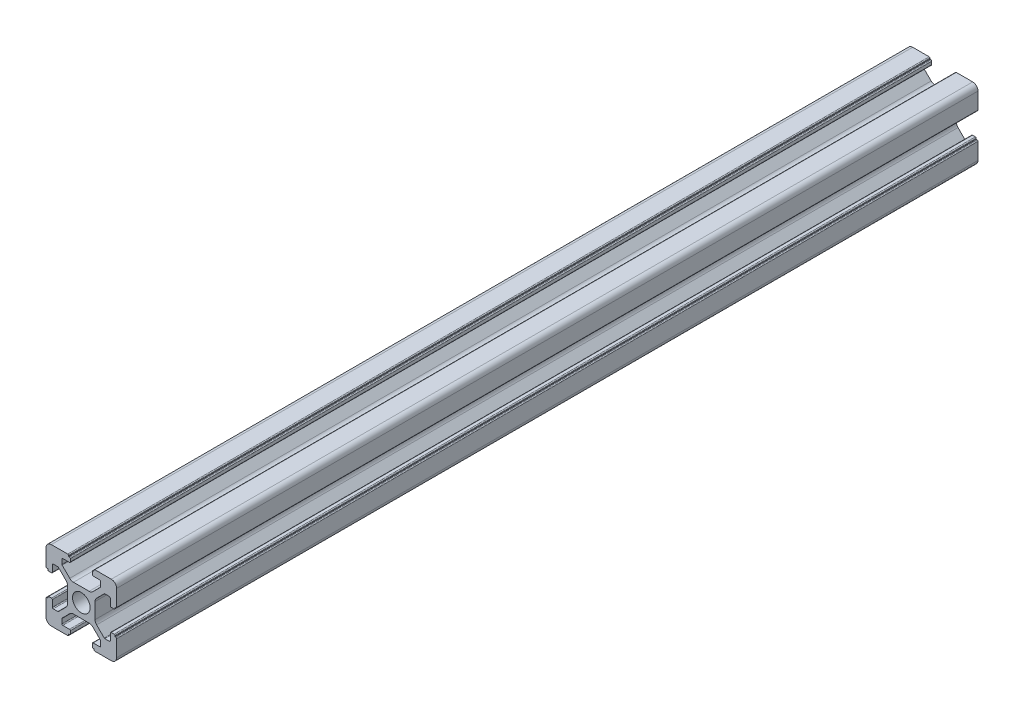
SolidWorks part; units mm, degrees
ref_plane "前视基准面" through (0, 0, 0) normal (0, 0, 1) x (1, 0, 0)
ref_plane "上视基准面" through (0, 0, 0) normal (0, 1, 0) x (1, 0, 0)
ref_plane "右视基准面" through (0, 0, 0) normal (1, 0, 0) x (0, 0, -1)
sketch "草图1" plane through (0, 0, 0) normal (0, 0, 1) x (1, 0, 0)
  line L0 (0, 0) -> (0, 5.5) construction
  line L1 (-8.5023, -10.0023) -> (-3.85, -10.0023)
  line L2 (-10.0023, -8.5023) -> (-10.0023, -3.85)
  line L3 (-8.5023, 10.0023) -> (-3.85, 10.0023)
  line L4 (10.0023, -8.5023) -> (10.0023, -3.85)
  line L5 (-10.0023, -10.0023) -> (10.0023, 10.0023) construction
  line L6 (-10.0023, 10.0023) -> (10.0023, -10.0023) construction
  line L7 (-2.218, -3.9) -> (2.218, -3.9)
  line L8 (-3.9, -2.218) -> (-3.9, 2.218)
  line L9 (-2.218, 3.9) -> (2.218, 3.9)
  line L10 (3.9, -2.218) -> (3.9, 2.218)
  line L11 (-3.9, -3.9) -> (3.9, 3.9) construction
  line L12 (-3.9, 3.9) -> (3.9, -3.9) construction
  line L13 (-5.25, -8.2) -> (-3.35, -8.2)
  line L14 (-8.2, -5.25) -> (-8.2, -3.35)
  line L15 (-5.25, 8.2) -> (-3.35, 8.2)
  line L16 (8.2, -5.25) -> (8.2, -3.35)
  line L17 (-8.2, -8.2) -> (8.2, 8.2) construction
  line L18 (-8.2, 8.2) -> (8.2, -8.2) construction
  line L19 (-7.95, 5.5) -> (-6.6642, 5.5)
  line L20 (0, 0) -> (5.5, 0) construction
  line L23 (-5.5, 7.95) -> (-5.5, 6.6642)
  line L26 (0, 0) -> (-0.5303, 0.5303)
  line L27 (3.2787, 4.3393) -> (5.4268, 6.4874)
  line L28 (0, 0) -> (0.5303, -0.5303)
  line L29 (5.5, 6.6642) -> (5.5, 7.95)
  line L30 (4.3393, 3.2787) -> (6.4874, 5.4268)
  line L31 (6.6642, 5.5) -> (7.95, 5.5)
  line L32 (4.3393, -3.2787) -> (6.4874, -5.4268)
  line L33 (3.2787, -4.3393) -> (5.4268, -6.4874)
  line L34 (-3.2787, -4.3393) -> (-5.4268, -6.4874)
  line L35 (-4.3393, -3.2787) -> (-6.4874, -5.4268)
  line L36 (-4.3393, 3.2787) -> (-6.4874, 5.4268)
  line L37 (-3.2787, 4.3393) -> (-5.4268, 6.4874)
  line L38 (3.1, -8.45) -> (3.1, -9.2523)
  line L39 (8.45, 3.1) -> (9.2523, 3.1)
  line L40 (-5.5, -6.6642) -> (-5.5, -7.95)
  line L41 (-6.6642, -5.5) -> (-7.95, -5.5)
  line L42 (5.5, -6.6642) -> (5.5, -7.95)
  line L43 (6.6642, -5.5) -> (7.95, -5.5)
  line L44 (9.2523, -3.1) -> (8.45, -3.1)
  line L46 (10.0023, 3.85) -> (10.0023, 8.5023)
  line L47 (8.2, 3.35) -> (8.2, 5.25)
  line L48 (-3.1, -9.2523) -> (-3.1, -8.45)
  line L49 (-8.45, -3.1) -> (-9.2523, -3.1)
  line L50 (-9.2523, 3.1) -> (-8.45, 3.1)
  line L51 (-3.1, 8.45) -> (-3.1, 9.2523)
  line L52 (3.1, 9.2523) -> (3.1, 8.45)
  line L53 (3.85, 10.0023) -> (8.5023, 10.0023)
  line L54 (3.35, 8.2) -> (5.25, 8.2)
  line L55 (-10.0023, 3.85) -> (-10.0023, 8.5023)
  line L56 (-8.2, 3.35) -> (-8.2, 5.25)
  line L57 (3.35, -8.2) -> (5.25, -8.2)
  line L58 (3.85, -10.0023) -> (8.5023, -10.0023)
  line L59 (9.7523, -3.6) -> (9.5023, -3.6)
  line L61 (9.7523, 3.6) -> (9.5023, 3.6)
  line L62 (9.5023, -3.6) -> (9.5023, -3.35)
  line L63 (3.6, -9.7523) -> (3.6, -9.5023)
  line L64 (3.35, -9.5023) -> (3.6, -9.5023)
  line L65 (9.5023, 3.35) -> (9.5023, 3.6)
  line L66 (-3.6, -9.5023) -> (-3.35, -9.5023)
  line L67 (-3.6, -9.7523) -> (-3.6, -9.5023)
  line L68 (-9.7523, -3.6) -> (-9.5023, -3.6)
  line L69 (-9.5023, -3.35) -> (-9.5023, -3.6)
  line L70 (-9.5023, 3.6) -> (-9.5023, 3.35)
  line L71 (-9.7523, 3.6) -> (-9.5023, 3.6)
  line L72 (-3.6, 9.7523) -> (-3.6, 9.5023)
  line L73 (-3.35, 9.5023) -> (-3.6, 9.5023)
  line L74 (3.6, 9.5023) -> (3.35, 9.5023)
  line L75 (3.6, 9.7523) -> (3.6, 9.5023)
  circle A0 centre (0, 0) radius 2.5
  arc A1 (10.0023, 8.5023) -> (8.5023, 10.0023) centre (8.5023, 8.5023) ccw
  arc A2 (8.5023, -10.0023) -> (10.0023, -8.5023) centre (8.5023, -8.5023) ccw
  arc A3 (-10.0023, -8.5023) -> (-8.5023, -10.0023) centre (-8.5023, -8.5023) ccw
  arc A4 (-10.0023, 8.5023) -> (-8.5023, 10.0023) centre (-8.5023, 8.5023) cw
  arc A5 (-9.5023, -3.35) -> (-9.2523, -3.1) centre (-9.2523, -3.35) cw
  arc A6 (-9.7523, -3.6) -> (-10.0023, -3.85) centre (-9.7523, -3.85) ccw
  arc A7 (-8.45, -3.1) -> (-8.2, -3.35) centre (-8.45, -3.35) cw
  arc A8 (-7.95, -5.5) -> (-8.2, -5.25) centre (-7.95, -5.25) cw
  arc A9 (-6.4874, -5.4268) -> (-6.6642, -5.5) centre (-6.6642, -5.25) cw
  arc A10 (-5.4268, -6.4874) -> (-5.5, -6.6642) centre (-5.25, -6.6642) ccw
  arc A11 (-5.5, -7.95) -> (-5.25, -8.2) centre (-5.25, -7.95) ccw
  arc A12 (-3.6, -9.7523) -> (-3.85, -10.0023) centre (-3.85, -9.7523) cw
  arc A13 (-3.35, -9.5023) -> (-3.1, -9.2523) centre (-3.35, -9.2523) ccw
  arc A14 (-3.1, -8.45) -> (-3.35, -8.2) centre (-3.35, -8.45) ccw
  arc A15 (3.1, -8.45) -> (3.35, -8.2) centre (3.35, -8.45) cw
  arc A16 (5.5, -7.95) -> (5.25, -8.2) centre (5.25, -7.95) cw
  arc A17 (5.4268, -6.4874) -> (5.5, -6.6642) centre (5.25, -6.6642) cw
  arc A18 (6.4874, -5.4268) -> (6.6642, -5.5) centre (6.6642, -5.25) ccw
  arc A19 (7.95, -5.5) -> (8.2, -5.25) centre (7.95, -5.25) ccw
  arc A20 (8.45, -3.1) -> (8.2, -3.35) centre (8.45, -3.35) ccw
  arc A21 (9.5023, -3.35) -> (9.2523, -3.1) centre (9.2523, -3.35) ccw
  arc A22 (9.7523, -3.6) -> (10.0023, -3.85) centre (9.7523, -3.85) cw
  arc A23 (3.35, -9.5023) -> (3.1, -9.2523) centre (3.35, -9.2523) cw
  arc A24 (3.6, -9.7523) -> (3.85, -10.0023) centre (3.85, -9.7523) ccw
  arc A25 (7.95, 5.5) -> (8.2, 5.25) centre (7.95, 5.25) cw
  arc A26 (8.2, 3.35) -> (8.45, 3.1) centre (8.45, 3.35) ccw
  arc A27 (9.5023, 3.35) -> (9.2523, 3.1) centre (9.2523, 3.35) cw
  arc A28 (9.7523, 3.6) -> (10.0023, 3.85) centre (9.7523, 3.85) ccw
  arc A29 (6.6642, 5.5) -> (6.4874, 5.4268) centre (6.6642, 5.25) ccw
  arc A30 (5.4268, 6.4874) -> (5.5, 6.6642) centre (5.25, 6.6642) ccw
  arc A31 (5.5, 7.95) -> (5.25, 8.2) centre (5.25, 7.95) ccw
  arc A32 (3.1, 8.45) -> (3.35, 8.2) centre (3.35, 8.45) ccw
  arc A33 (3.6, 9.7523) -> (3.85, 10.0023) centre (3.85, 9.7523) cw
  arc A34 (3.35, 9.5023) -> (3.1, 9.2523) centre (3.35, 9.2523) ccw
  arc A35 (-9.7523, 3.6) -> (-10.0023, 3.85) centre (-9.7523, 3.85) cw
  arc A36 (-9.5023, 3.35) -> (-9.2523, 3.1) centre (-9.2523, 3.35) ccw
  arc A37 (-8.45, 3.1) -> (-8.2, 3.35) centre (-8.45, 3.35) ccw
  arc A38 (-8.2, 5.25) -> (-7.95, 5.5) centre (-7.95, 5.25) cw
  arc A39 (-6.4874, 5.4268) -> (-6.6642, 5.5) centre (-6.6642, 5.25) ccw
  arc A40 (-5.4268, 6.4874) -> (-5.5, 6.6642) centre (-5.25, 6.6642) cw
  arc A41 (-5.5, 7.95) -> (-5.25, 8.2) centre (-5.25, 7.95) cw
  arc A42 (-3.1, 8.45) -> (-3.35, 8.2) centre (-3.35, 8.45) cw
  arc A43 (-3.1, 9.2523) -> (-3.35, 9.5023) centre (-3.35, 9.2523) ccw
  arc A44 (-3.6, 9.7523) -> (-3.85, 10.0023) centre (-3.85, 9.7523) ccw
  arc A45 (-4.3393, 3.2787) -> (-3.9, 2.218) centre (-5.4, 2.218) cw
  arc A46 (-3.2787, 4.3393) -> (-2.218, 3.9) centre (-2.218, 5.4) ccw
  arc A47 (3.2787, 4.3393) -> (2.218, 3.9) centre (2.218, 5.4) cw
  arc A48 (4.3393, 3.2787) -> (3.9, 2.218) centre (5.4, 2.218) ccw
  arc A49 (4.3393, -3.2787) -> (3.9, -2.218) centre (5.4, -2.218) cw
  arc A50 (3.2787, -4.3393) -> (2.218, -3.9) centre (2.218, -5.4) ccw
  arc A51 (-4.3393, -3.2787) -> (-3.9, -2.218) centre (-5.4, -2.218) ccw
  arc A52 (-2.218, -3.9) -> (-3.2787, -4.3393) centre (-2.218, -5.4) ccw
  point P0 (0, 0)
  point P7 (10.0023, 0)
  point P62 (0, 0)
  point P76 (0, 0)
  point P92 (-8.2, -5.5)
  point P99 (0, 0)
  point P106 (-5.5, -8.2)
  point P117 (5.5, -8.2)
  point P124 (8.2, -5.5)
  point P137 (8.2, 5.5)
  point P140 (8.2, 3.1)
  point P147 (6.5607, 5.5)
  point P152 (5.5, 8.2)
  point P167 (-8.2, 5.5)
  point P174 (-5.5, 8.2)
  dimension "D1" = 1.5
  dimension "D5" = 0.25
  dimension "D6" = 1.5
  dimension "D2" = 4
  dimension "D3" = 4
  dimension "D4" = 4
extrude "凸台-拉伸1" add sketch "草图1" along normal blind 244 contours A52 L7 A50 L33 A17 L42 A16 L57 A15 L38 A23 L64 L63 A24 L58 A2 L4 A22 L59 L62 A21 L44 A20 L16 A19 L43 A18 L32 A49 L10 A48 L30 A29 L31 A25 L47 A26 L39 A27 L65 L61 A28 L46 A1 L53 A33 L75 L74 A34 L52 A32
ref_plane "Plane1" through (0, 0, 122) normal (0, 0, 1) x (1, 0, 0)
